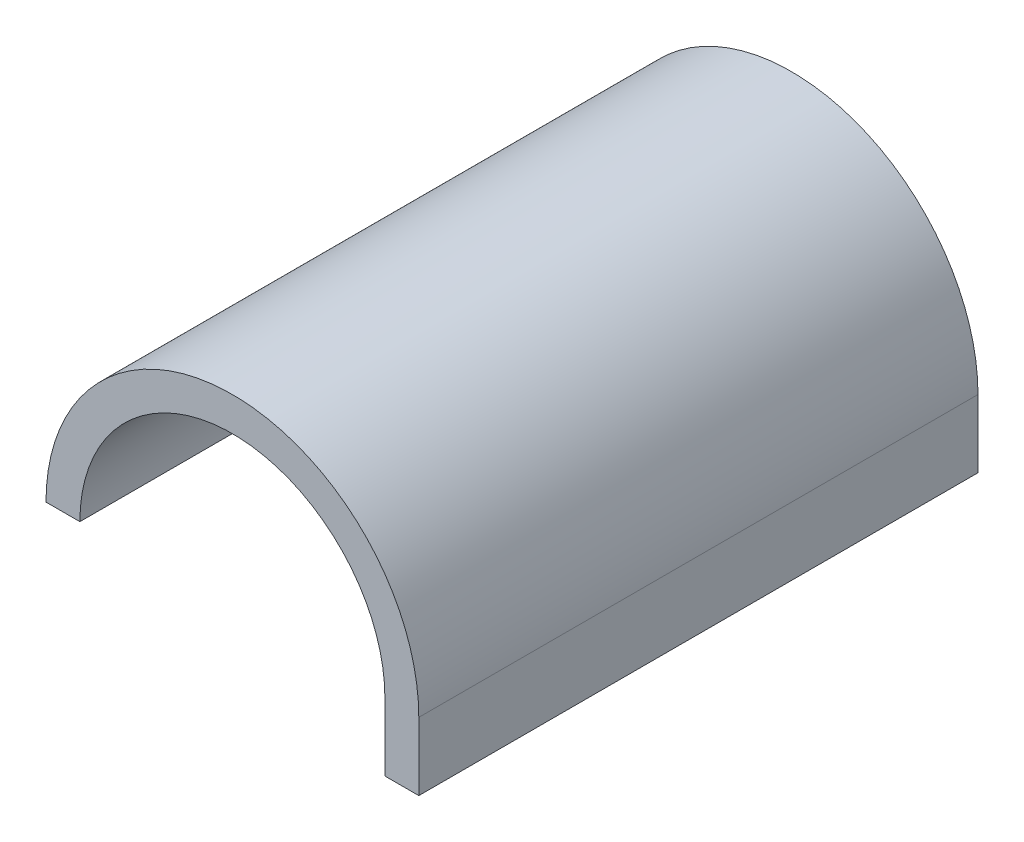
SolidWorks part; units mm, degrees
ref_plane "Front Plane" through (0, 0, 0) normal (0, 0, 1) x (1, 0, 0)
ref_plane "Top Plane" through (0, 0, 0) normal (0, 1, 0) x (1, 0, 0)
ref_plane "Right Plane" through (0, 0, 0) normal (1, 0, 0) x (0, 0, -1)
sketch "Sketch1" plane through (0, 0, 0) normal (0, 1, 0) x (1, 0, 0)
  line L1 (39.5, -82.5) -> (-39.5, -82.5) construction
  line L2 (39.5, -82.5) -> (39.5, 82.5) construction
  line L3 (39.5, 82.5) -> (-39.5, 82.5) construction
  line L4 (-39.5, -82.5) -> (-39.5, 82.5) construction
  line L5 (39.5, -82.5) -> (-39.5, 82.5) construction
  line L6 (39.5, 82.5) -> (-39.5, -82.5) construction
  point P0 (0, 0)
  dimension "D1" = 79
  dimension "D2" = 165
sketch "Sketch2" plane through (0, 0, 0) normal (0, 0, 1) x (1, 0, 0)
  line L0 (39.5, 0) -> (-39.5, 0) construction
  line L1 (39.5, 0) -> (-39.5, 0) construction
  line L2 (39.5, 0) -> (-39.5, 0) construction
  line L3 (-55, 0) -> (-45, 0)
  line L4 (45, 0) -> (55, 0)
  arc A0 (-45, 0) -> (45, 0) centre (0, 0) cw
  arc A1 (-55, 0) -> (55, 0) centre (0, 0) cw
  dimension "D1" = 45
  dimension "D2" = 10
extrude "Boss-Extrude1" add sketch "Sketch2" along normal mid plane 165
sketch "Sketch3" plane through (0, 0, 0) normal (0, -1, 0) x (1, 0, 0)
  line L4 (45, -82.5) -> (55, -82.5)
  line L5 (55, -82.5) -> (55, 82.5)
  line L6 (55, 82.5) -> (45, 82.5)
  line L7 (45, 82.5) -> (45, -82.5)
  line L8 (45, -82.5) -> (55, -82.5)
  line L9 (55, -82.5) -> (55, 82.5)
  line L10 (55, 82.5) -> (45, 82.5)
  line L11 (45, 82.5) -> (45, -82.5)
  dimension "D1" = 0
extrude "Boss-Extrude2" add sketch "Sketch3" along normal blind 20
